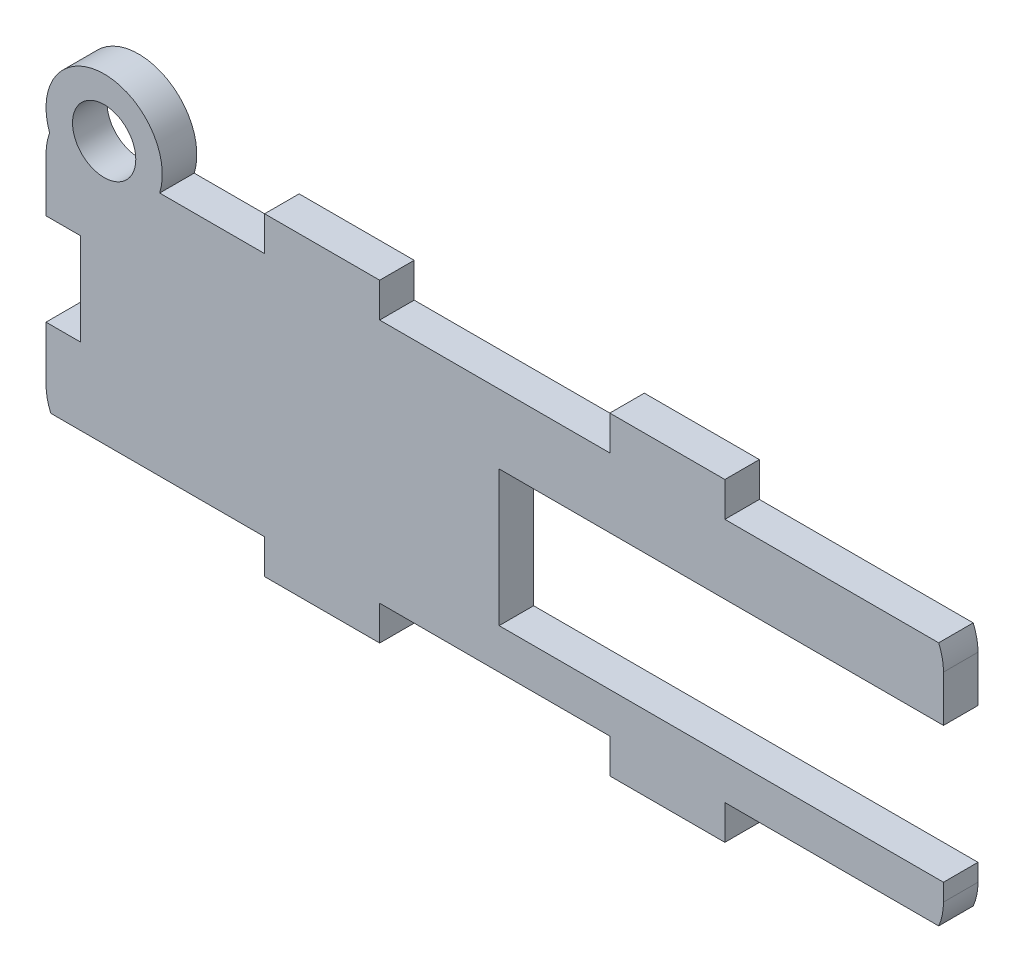
SolidWorks part; units mm, degrees
ref_plane "Front Plane" through (0, 0, 0) normal (0, 0, 1) x (1, 0, 0)
ref_plane "Top Plane" through (0, 0, 0) normal (0, 1, 0) x (1, 0, 0)
ref_plane "Right Plane" through (0, 0, 0) normal (1, 0, 0) x (0, 0, -1)
sketch "Sketch1" plane through (0, 0, 0) normal (0, 0, 1) x (1, 0, 0)
  line L0 (52, -3) -> (52, 0) construction
  line L1 (-7, -3) -> (3, -3)
  line L2 (-26, 2) -> (-26, 19.3118)
  line L3 (-7, 24.3118) -> (3, 24.3118)
  line L4 (52, 2) -> (52, 19.3118)
  line L5 (-26, -3) -> (52, 24.3118) construction
  line L6 (-26, 24.3118) -> (52, -3) construction
  line L7 (23, -3) -> (33, -3)
  line L8 (-7, 0) -> (-25.5826, 0)
  line L9 (-7, 0) -> (-7, -3)
  line L12 (-7, 0) -> (-26, -3) construction
  line L13 (-7, -3) -> (-26, 0) construction
  line L15 (3, -3) -> (3, 0)
  line L16 (3, 0) -> (23, 0)
  line L17 (23, -3) -> (23, 0)
  line L18 (3, -3) -> (23, 0) construction
  line L19 (3, 0) -> (23, -3) construction
  line L21 (33, -3) -> (33, 0)
  line L22 (33, 0) -> (51.5826, 0)
  line L24 (33, -3) -> (52, 0) construction
  line L25 (33, 0) -> (52, -3) construction
  line L27 (-33.6771, 10.6559) -> (59.6771, 10.6559) construction
  line L28 (33, 24.3118) -> (33, 21.3118)
  line L29 (23, 24.3118) -> (33, 24.3118)
  line L30 (23, 24.3118) -> (23, 21.3118)
  line L31 (3, 24.3118) -> (3, 21.3118)
  line L32 (-7, 21.3118) -> (-7, 24.3118)
  line L33 (3, 0) -> (-7, 0) construction
  line L34 (-7, 21.3118) -> (-25.5826, 21.3118)
  line L35 (3, 21.3118) -> (23, 21.3118)
  line L36 (33, 21.3118) -> (51.5826, 21.3118)
  line L37 (-7, 0) -> (-10, 0) construction
  arc A1 (-26, 19.3118) -> (-25.5826, 21.3118) centre (-21, 19.3118) cw
  arc A2 (51.5826, 21.3118) -> (52, 19.3118) centre (47, 19.3118) cw
  arc A4 (-25.5826, 0) -> (-26, 2) centre (-21, 2) cw
  arc A5 (51.5826, 0) -> (52, 2) centre (47, 2) ccw
  point P4 (13, 10.6559)
  point P24 (-16.5, -1.5)
  point P29 (13, -1.5)
  point P35 (42.5, -1.5)
  point P41 (13, 10.6559)
extrude "Boss-Extrude1" add sketch "Sketch1" along normal blind 3
sketch "Sketch2" plane through (0, 0, 3) normal (0, 0, 1) x (1, 0, 0)
  line L0 (13.38, 3.5) -> (13.38, 15.3) construction
  line L1 (13.38, 15.3) -> (23.54, 15.3) construction
  line L2 (13.38, 3.5) -> (13.38, 15.3)
  line L3 (13.38, 15.3) -> (23.54, 15.3)
  line L4 (23.54, 15.3) -> (52, 15.3)
  line L5 (52, 2) -> (52, 19.3118) construction
  line L7 (13.38, 3.5) -> (52, 3.5)
  line L8 (52, 3.5) -> (52, 15.3)
extrude "Cut-Extrude1" cut sketch "Sketch2" against normal up to next
sketch "Sketch3" plane through (0, 0, 3) normal (0, 0, 1) x (1, 0, 0)
  line L0 (-7, 22.8118) -> (-23, 22.8118) construction
  line L1 (-7, 24.3118) -> (-7, 21.3118) construction
  line L2 (-23, 24.3118) -> (-23, 21.3118) construction
  line L4 (-7, 21.3118) -> (-25.5826, 21.3118) construction
  circle A4 centre (-20.9461, 22.8118) radius 2.75
  circle A5 centre (-20.9461, 22.8118) radius 5.0539
  point P8 (0, 0)
  dimension "D1" = 5.5
  dimension "D2" = 10.1078
extrude "Boss-Extrude2" add sketch "Sketch3" against normal blind 3
sketch "Sketch4" plane through (0, 0, 3) normal (0, 0, 1) x (1, 0, 0)
  line L0 (-23.251, 21.3118) -> (-18.6412, 21.3118)
  line L2 (-20.9461, 21.3118) -> (-20.9461, 25.5618) construction
  arc A1 (-18.6412, 21.3118) -> (-23.251, 21.3118) centre (-20.9461, 22.8118) ccw construction
  arc A2 (-23.251, 21.3118) -> (-18.6412, 21.3118) centre (-20.9461, 22.8118) ccw
extrude "Cut-Extrude2" cut sketch "Sketch4" against normal up to next
sketch "Sketch5" plane through (0, 0, 3) normal (0, 0, 1) x (1, 0, 0)
  line L0 (-26, 19.3118) -> (-26, 2) construction
  line L1 (-23, 6.6559) -> (-26, 6.6559)
  line L2 (-23, 6.6559) -> (-23, 14.6559)
  line L3 (-23, 14.6559) -> (-26, 14.6559)
  line L4 (-26, 6.6559) -> (-26, 14.6559)
  line L5 (-23, 6.6559) -> (-26, 14.6559) construction
  line L6 (-23, 14.6559) -> (-26, 6.6559) construction
  point P4 (-24.5, 10.6559)
  dimension "D1" = 8
extrude "Cut-Extrude3" cut sketch "Sketch5" against normal blind 3 contours L2 L3 L4 L1
